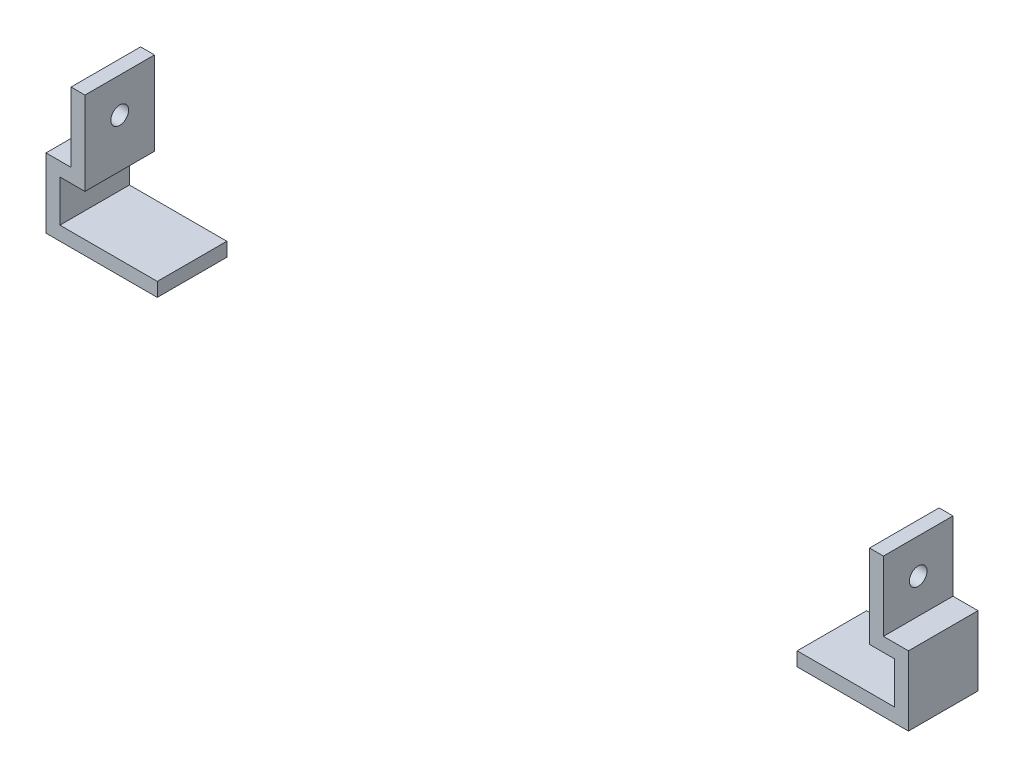
SolidWorks part; units mm, degrees
ref_plane "Front Plane" through (0, 0, 0) normal (0, 0, 1) x (1, 0, 0)
ref_plane "Top Plane" through (0, 0, 0) normal (0, 1, 0) x (1, 0, 0)
ref_plane "Right Plane" through (0, 0, 0) normal (1, 0, 0) x (0, 0, -1)
sketch "Sketch1" plane through (0, 0, 0) normal (0, 0, 1) x (1, 0, 0)
  line L1 (141, -15) -> (-141, -15)
  line L2 (141, -15) -> (141, 15)
  line L3 (141, 15) -> (-141, 15)
  line L4 (-141, -15) -> (-141, 15)
  line L5 (141, -15) -> (-141, 15) construction
  line L6 (141, 15) -> (-141, -15) construction
  line L7 (-141, -15) -> (-146, -15)
  line L8 (-141, -15) -> (-141, 15)
  line L9 (-141, 15) -> (-146, 15)
  line L10 (-146, -15) -> (-146, 15)
  line L11 (141, -15) -> (146, -15)
  line L12 (141, -15) -> (141, 15)
  line L13 (141, 15) -> (146, 15)
  line L14 (146, -15) -> (146, 15)
  line L15 (0, -15) -> (-150, -15)
  line L16 (0, -15) -> (0, -30)
  line L17 (0, -30) -> (-150, -30)
  line L18 (-150, -15) -> (-150, -30)
  line L19 (0, -15) -> (150, -15)
  line L20 (0, -15) -> (0, -30)
  line L21 (0, -30) -> (150, -30)
  line L22 (150, -15) -> (150, -30)
  line L23 (-141, -15) -> (-150, -15)
  line L24 (-141, -15) -> (-141, -10)
  line L25 (-141, -10) -> (-150, -10)
  line L26 (-150, -15) -> (-150, -10)
  line L27 (141, -15) -> (150, -15)
  line L28 (141, -15) -> (141, -10)
  line L29 (141, -10) -> (150, -10)
  line L30 (150, -15) -> (150, -10)
  line L31 (-150, -10) -> (-155, -10)
  line L32 (-150, -10) -> (-150, -30)
  line L33 (-150, -30) -> (-155, -30)
  line L34 (-155, -10) -> (-155, -30)
  line L35 (150, -10) -> (155, -10)
  line L36 (150, -10) -> (150, -30)
  line L37 (150, -30) -> (155, -30)
  line L38 (155, -10) -> (155, -30)
  line L39 (-155, -30) -> (-115, -30)
  line L40 (-155, -30) -> (-155, -35)
  line L41 (-155, -35) -> (-115, -35)
  line L42 (-115, -30) -> (-115, -35)
  line L43 (155, -30) -> (115, -30)
  line L44 (155, -30) -> (155, -35)
  line L45 (155, -35) -> (115, -35)
  line L46 (115, -30) -> (115, -35)
  point P0 (0, 0)
  dimension "D1" = 282
  dimension "D2" = 30
  dimension "D3" = 5
  dimension "D4" = 5
  dimension "D5" = 5
  dimension "D6" = 150
  dimension "D7" = 5
  dimension "D8" = 5
  dimension "D9" = 5
  dimension "D10" = 5
  dimension "D11" = 40
  dimension "D12" = 15
extrude "Boss-Extrude1" add sketch "Sketch1" along normal blind 25 contours L42 L17 L33 L40 L41 | L31 L34 L33 L18 L26 | L26 L15 L10 L25 | L4 L25 L10 L7 | L25 L8 L9 L10 | L21 L46 L45 L44 L37 | L38 L35 L30 L22 L37 | L19 L30 L29 L14 | L29 L2 L11 L14 | L12 L29 L14 L13
sketch "Sketch2" plane through (146, 0, 0) normal (1, 0, 0) x (0, 0, -1)
  line L0 (0, 15) -> (-25, -10)
  circle A0 centre (-12.5, 2.5) radius 3.175
  dimension "D1" = 6.35
extrude "Cut-Extrude1" cut sketch "Sketch2" against normal through all contours A0
